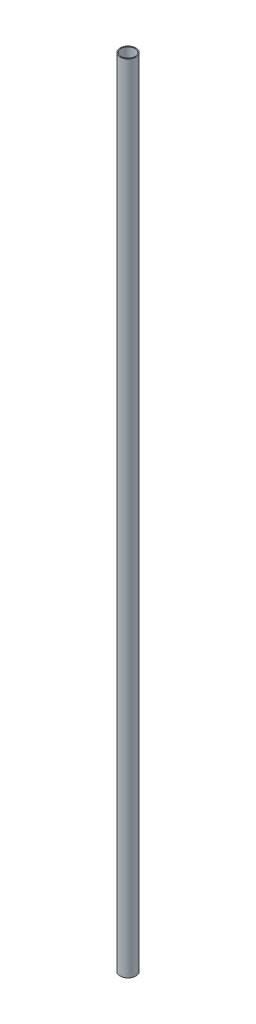
SolidWorks part; units mm, degrees
ref_plane "Front Plane" through (0, 0, 0) normal (0, 0, 1) x (1, 0, 0)
ref_plane "Top Plane" through (0, 0, 0) normal (0, 1, 0) x (1, 0, 0)
ref_plane "Right Plane" through (0, 0, 0) normal (1, 0, 0) x (0, 0, -1)
sketch "Sketch1" plane through (0, 0, 0) normal (0, 1, 0) x (1, 0, 0)
  circle A0 centre (0, 0) radius 4
  circle A1 centre (0, 0) radius 3.5
  dimension "D1" = 8
  dimension "D2" = 7
extrude "Boss-Extrude1" add sketch "Sketch1" along normal blind 400
